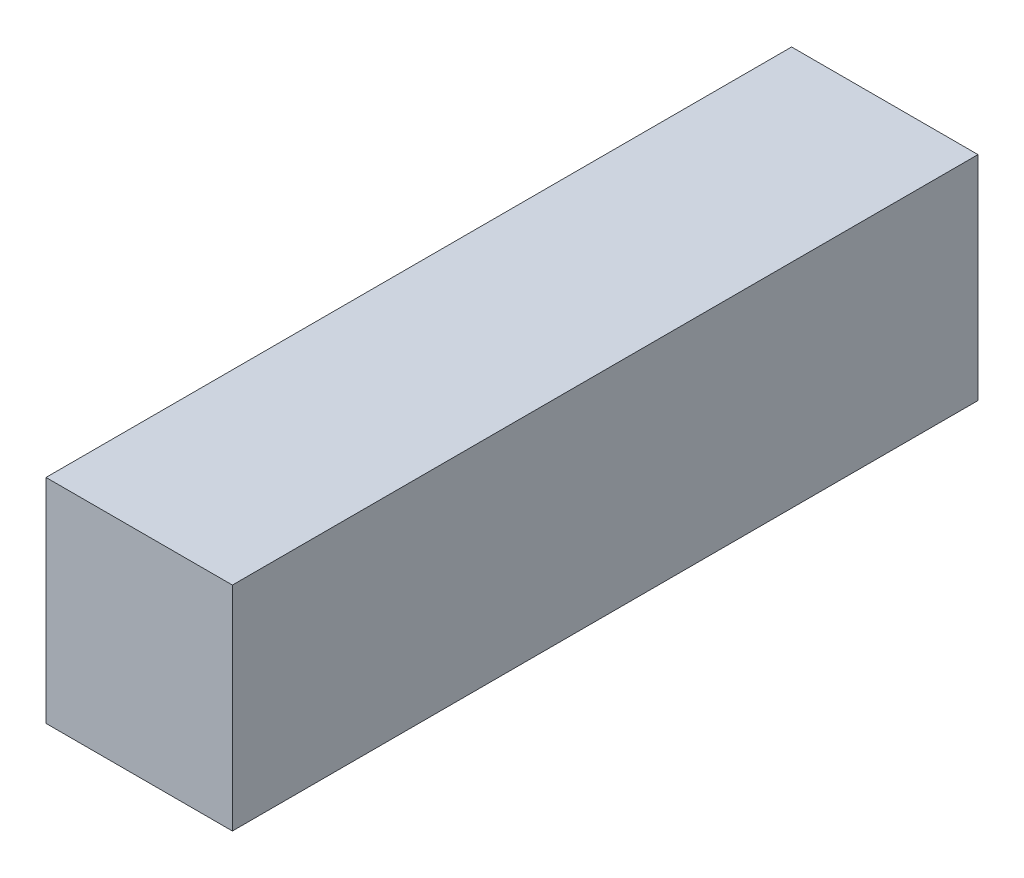
SolidWorks part; units mm, degrees
ref_plane "Front Plane" through (0, 0, 0) normal (0, 0, 1) x (1, 0, 0)
ref_plane "Top Plane" through (0, 0, 0) normal (0, 1, 0) x (1, 0, 0)
ref_plane "Right Plane" through (0, 0, 0) normal (1, 0, 0) x (0, 0, -1)
sketch "Sketch1" plane through (0, 0, 0) normal (0, 1, 0) x (1, 0, 0)
  line L1 (-17.5, -70) -> (17.5, -70)
  line L2 (-17.5, -70) -> (-17.5, 70)
  line L3 (-17.5, 70) -> (17.5, 70)
  line L4 (17.5, -70) -> (17.5, 70)
  line L5 (-17.5, -70) -> (17.5, 70) construction
  line L6 (-17.5, 70) -> (17.5, -70) construction
  point P0 (0, 0)
extrude "Boss-Extrude1" add sketch "Sketch1" along normal blind 40
